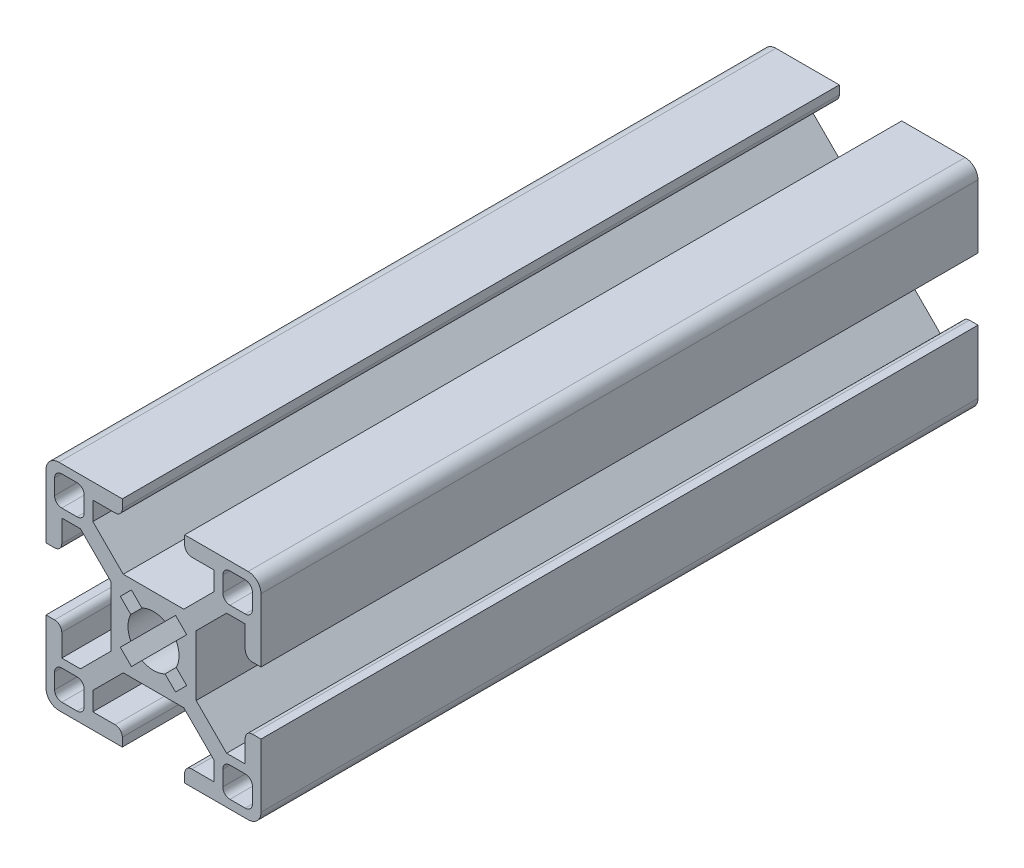
SolidWorks part; units mm, degrees
ref_plane "Front Plane" through (0, 0, 0) normal (0, 0, 1) x (1, 0, 0)
ref_plane "Top Plane" through (0, 0, 0) normal (0, 1, 0) x (1, 0, 0)
ref_plane "Right Plane" through (0, 0, 0) normal (1, 0, 0) x (0, 0, -1)
sketch "Sketch1" plane through (0, 0, 0) normal (0, 0, 1) x (1, 0, 0)
  line L0 (0, 0) -> (5.95, 0) construction
  line L1 (0, 0) -> (0, 5.95) construction
  line L2 (-5.95, 5.95) -> (5.95, 5.95)
  line L3 (5.95, 5.95) -> (5.95, 0)
  line L4 (4.2176, 5.95) -> (8.4602, 10.1926)
  line L5 (5.95, 5.95) -> (8.4425, 8.4425) construction
  line L6 (5.95, 4.2176) -> (10.1926, 8.4602)
  line L7 (8.4602, 12.7926) -> (8.4602, 8.4602)
  line L8 (8.4602, 8.4602) -> (12.7926, 8.4602)
  line L9 (12.7926, 8.4602) -> (12.7926, 5.3502)
  line L10 (13.7926, 4.3502) -> (14.9926, 4.3502)
  line L11 (14.9926, 4.3502) -> (14.9926, 13.1926)
  line L12 (8.4602, 8.4602) -> (14.9926, 14.9926) construction
  line L13 (4.3502, 13.7926) -> (4.3502, 14.9926)
  line L14 (4.3502, 14.9926) -> (13.1926, 14.9926)
  line L15 (5.3502, 12.7926) -> (8.4602, 12.7926)
  line L16 (-9.6602, 9.6602) -> (-13.7926, 13.7926) construction
  line L17 (10.6602, 13.7926) -> (12.7926, 13.7926)
  line L18 (9.6602, 12.7926) -> (9.6602, 10.6602)
  line L19 (10.6602, 9.6602) -> (12.7926, 9.6602)
  line L20 (13.7926, 12.7926) -> (13.7926, 10.6602)
  line L21 (9.6602, 13.7926) -> (13.7926, 9.6602) construction
  line L22 (9.6602, 9.6602) -> (13.7926, 13.7926) construction
  line L23 (-9.6602, 13.7926) -> (-13.7926, 9.6602) construction
  line L24 (-8.4602, 8.4602) -> (-14.9926, 14.9926) construction
  line L25 (-5.95, 5.95) -> (-8.4425, 8.4425) construction
  line L26 (-13.7926, 12.7926) -> (-13.7926, 10.6602)
  line L27 (-10.6602, 9.6602) -> (-12.7926, 9.6602)
  line L28 (-9.6602, 12.7926) -> (-9.6602, 10.6602)
  line L29 (-10.6602, 13.7926) -> (-12.7926, 13.7926)
  line L30 (-5.3502, 12.7926) -> (-8.4602, 12.7926)
  line L31 (-4.3502, 14.9926) -> (-13.1926, 14.9926)
  line L32 (-4.3502, 13.7926) -> (-4.3502, 14.9926)
  line L33 (-14.9926, 4.3502) -> (-14.9926, 13.1926)
  line L34 (-13.7926, 4.3502) -> (-14.9926, 4.3502)
  line L35 (-12.7926, 8.4602) -> (-12.7926, 5.3502)
  line L36 (-8.4602, 8.4602) -> (-12.7926, 8.4602)
  line L37 (-8.4602, 12.7926) -> (-8.4602, 8.4602)
  line L38 (-5.95, 4.2176) -> (-10.1926, 8.4602)
  line L39 (-4.2176, 5.95) -> (-8.4602, 10.1926)
  line L40 (-5.95, 5.95) -> (-5.95, 0)
  line L41 (-5.95, 0) -> (5.95, 0)
  arc A0 (13.1926, 14.9926) -> (14.9926, 13.1926) centre (13.1926, 13.1926) cw
  arc A1 (10.6602, 13.7926) -> (9.6602, 12.7926) centre (10.6602, 12.7926) ccw
  arc A2 (12.7926, 13.7926) -> (13.7926, 12.7926) centre (12.7926, 12.7926) cw
  arc A3 (12.7926, 9.6602) -> (13.7926, 10.6602) centre (12.7926, 10.6602) ccw
  arc A4 (9.6602, 10.6602) -> (10.6602, 9.6602) centre (10.6602, 10.6602) ccw
  arc A5 (4.3502, 13.7926) -> (5.3502, 12.7926) centre (5.3502, 13.7926) ccw
  arc A6 (12.7926, 5.3502) -> (13.7926, 4.3502) centre (13.7926, 5.3502) ccw
  arc A7 (-12.7926, 5.3502) -> (-13.7926, 4.3502) centre (-13.7926, 5.3502) cw
  arc A8 (-4.3502, 13.7926) -> (-5.3502, 12.7926) centre (-5.3502, 13.7926) cw
  arc A9 (-9.6602, 10.6602) -> (-10.6602, 9.6602) centre (-10.6602, 10.6602) cw
  arc A10 (-12.7926, 9.6602) -> (-13.7926, 10.6602) centre (-12.7926, 10.6602) cw
  arc A11 (-12.7926, 13.7926) -> (-13.7926, 12.7926) centre (-12.7926, 12.7926) ccw
  arc A12 (-10.6602, 13.7926) -> (-9.6602, 12.7926) centre (-10.6602, 12.7926) cw
  arc A13 (-13.1926, 14.9926) -> (-14.9926, 13.1926) centre (-13.1926, 13.1926) ccw
  point P12 (11.7264, 11.7264)
  point P40 (4.3502, 12.7926)
  point P43 (12.7926, 4.3502)
  point P82 (-12.7926, 4.3502)
  point P83 (-4.3502, 12.7926)
  point P84 (-11.7264, 11.7264)
  dimension "D9" = 1.8
  dimension "D10" = 1
  dimension "D11" = 1
  dimension "D1" = 5.95
  dimension "D4" = 2.6
  dimension "D2" = 135
  dimension "D3" = 2.45
  dimension "D5" = 6
  dimension "D6" = 4.11
  dimension "D7" = 2.2
  dimension "D8" = 1.2
extrude "Boss-Extrude1" add sketch "Sketch1" against normal blind 100 contours L31 A13 L33 L34 A7 L35 L36 L37 L30 A8 L32 L29 A12 L28 A9 L27 A10 L26 A11 | L40 L2 L39 L37 L36 L38 | L40 L41 L3 L2 | L8 L7 L4 L2 L3 L6 | L9 A6 L10 L11 A0 L14 L13 A5 L15 L7 L8 A4 L18 A1 L17 A2 L20 A3 L19
mirror "Mirror1" about plane through (0, 0, -100) normal (0, -1, 0) of bodies 101
sketch "Sketch2" plane through (0, 0, 0) normal (0, 0, 1) x (1, 0, 0)
  line L0 (-3.0759, -4.6315) -> (4.6315, 3.0759)
  line L1 (-3.0759, -4.6315) -> (-4.6315, -3.0759)
  line L2 (4.6315, 3.0759) -> (3.0759, 4.6315)
  line L3 (-4.6315, -3.0759) -> (3.0759, 4.6315)
  line L4 (-3.0759, -4.6315) -> (3.0759, 4.6315) construction
  line L5 (4.6315, 3.0759) -> (-4.6315, -3.0759) construction
  line L6 (0, 0) -> (0, 2.5254) construction
  line L7 (-4.6315, 3.0759) -> (3.0759, -4.6315)
  line L8 (-4.6315, 3.0759) -> (-3.0759, 4.6315)
  line L9 (-3.0759, 4.6315) -> (4.6315, -3.0759)
  line L10 (3.0759, -4.6315) -> (4.6315, -3.0759)
  line L11 (0, 0) -> (3.0759, 4.6315) construction
  line L12 (0, 0) -> (4.6315, -3.0759) construction
  circle A0 centre (0, 0) radius 3.555
  dimension "D1" = 7.11
  dimension "D2" = 45
  dimension "D3" = 2.2
  dimension "D4" = 10.9
  dimension "D6" = 90
  dimension "D5" = 2
extrude "Cut-Extrude1" cut sketch "Sketch2" against normal through all contours A0 L9 L8 L7 | L9 A0 L7 L3 | L7 A0 L3 | A0 L3 L1 L0 | L3 A0 L0 L7 | L0 A0 L7 | L7 A0 L9 L0 | L9 A0 L0 | L9 L3 L7 L0 | L0 A0 L3 L9 | L3 A0 L9 | A0 L0 L2 L3 | A0 L7 L10 L9
